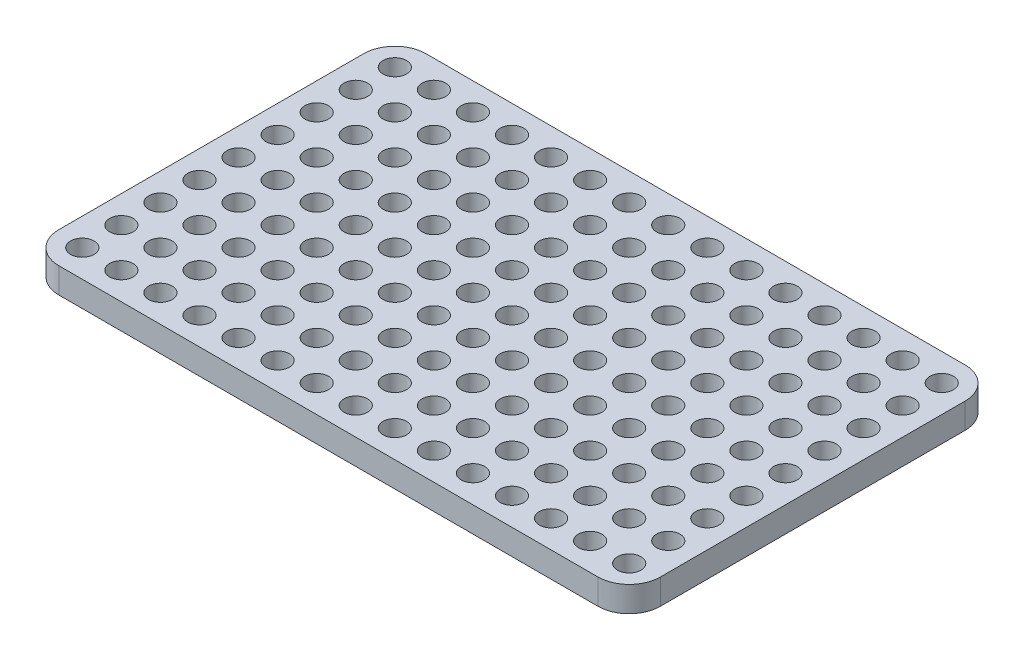
SolidWorks part; units mm, degrees
material "ABS"
ref_plane "Front Plane" through (0, 0, 0) normal (0, 0, 1) x (1, 0, 0)
ref_plane "Top Plane" through (0, 0, 0) normal (0, 1, 0) x (1, 0, 0)
ref_plane "Right Plane" through (0, 0, 0) normal (1, 0, 0) x (0, 0, -1)
sketch "Sketch1" plane through (0, 0, 0) normal (0, 1, 0) x (1, 0, 0)
  line L0 (-38.5, 23.5) -> (38.5, -23.5) construction
  line L1 (-34.5, 23.5) -> (34.5, 23.5)
  line L2 (-38.5, 19.5) -> (-38.5, -19.5)
  line L3 (-34.5, -23.5) -> (34.5, -23.5)
  line L4 (38.5, 19.5) -> (38.5, -19.5)
  circle A0 centre (-35, -20) radius 1.5025
  circle A1 centre (-30, -20) radius 1.5025
  circle A2 centre (-25, -20) radius 1.5025
  circle A3 centre (-20, -20) radius 1.5025
  circle A4 centre (-15, -20) radius 1.5025
  circle A5 centre (-10, -20) radius 1.5025
  circle A6 centre (-5, -20) radius 1.5025
  circle A7 centre (0, -20) radius 1.5025
  circle A8 centre (5, -20) radius 1.5025
  circle A9 centre (10, -20) radius 1.5025
  circle A10 centre (15, -20) radius 1.5025
  circle A11 centre (20, -20) radius 1.5025
  circle A12 centre (25, -20) radius 1.5025
  circle A13 centre (30, -20) radius 1.5025
  circle A14 centre (35, -20) radius 1.5025
  circle A15 centre (-35, -15) radius 1.5025
  circle A16 centre (-30, -15) radius 1.5025
  circle A17 centre (-25, -15) radius 1.5025
  circle A18 centre (-20, -15) radius 1.5025
  circle A19 centre (-15, -15) radius 1.5025
  circle A20 centre (-10, -15) radius 1.5025
  circle A21 centre (-5, -15) radius 1.5025
  circle A22 centre (0, -15) radius 1.5025
  circle A23 centre (5, -15) radius 1.5025
  circle A24 centre (10, -15) radius 1.5025
  circle A25 centre (15, -15) radius 1.5025
  circle A26 centre (20, -15) radius 1.5025
  circle A27 centre (25, -15) radius 1.5025
  circle A28 centre (30, -15) radius 1.5025
  circle A29 centre (35, -15) radius 1.5025
  circle A30 centre (-35, -10) radius 1.5025
  circle A31 centre (-30, -10) radius 1.5025
  circle A32 centre (-25, -10) radius 1.5025
  circle A33 centre (-20, -10) radius 1.5025
  circle A34 centre (-15, -10) radius 1.5025
  circle A35 centre (-10, -10) radius 1.5025
  circle A36 centre (-5, -10) radius 1.5025
  circle A37 centre (0, -10) radius 1.5025
  circle A38 centre (5, -10) radius 1.5025
  circle A39 centre (10, -10) radius 1.5025
  circle A40 centre (15, -10) radius 1.5025
  circle A41 centre (20, -10) radius 1.5025
  circle A42 centre (25, -10) radius 1.5025
  circle A43 centre (30, -10) radius 1.5025
  circle A44 centre (35, -10) radius 1.5025
  circle A45 centre (-35, -5) radius 1.5025
  circle A46 centre (-30, -5) radius 1.5025
  circle A47 centre (-25, -5) radius 1.5025
  circle A48 centre (-20, -5) radius 1.5025
  circle A49 centre (-15, -5) radius 1.5025
  circle A50 centre (-10, -5) radius 1.5025
  circle A51 centre (-5, -5) radius 1.5025
  circle A52 centre (0, -5) radius 1.5025
  circle A53 centre (5, -5) radius 1.5025
  circle A54 centre (10, -5) radius 1.5025
  circle A55 centre (15, -5) radius 1.5025
  circle A56 centre (20, -5) radius 1.5025
  circle A57 centre (25, -5) radius 1.5025
  circle A58 centre (30, -5) radius 1.5025
  circle A59 centre (35, -5) radius 1.5025
  circle A60 centre (-35, 0) radius 1.5025
  circle A61 centre (-30, 0) radius 1.5025
  circle A62 centre (-25, 0) radius 1.5025
  circle A63 centre (-20, 0) radius 1.5025
  circle A64 centre (-15, 0) radius 1.5025
  circle A65 centre (-10, 0) radius 1.5025
  circle A66 centre (-5, 0) radius 1.5025
  circle A67 centre (0, 0) radius 1.5025
  circle A68 centre (5, 0) radius 1.5025
  circle A69 centre (10, 0) radius 1.5025
  circle A70 centre (15, 0) radius 1.5025
  circle A71 centre (20, 0) radius 1.5025
  circle A72 centre (25, 0) radius 1.5025
  circle A73 centre (30, 0) radius 1.5025
  circle A74 centre (35, 0) radius 1.5025
  circle A75 centre (-35, 5) radius 1.5025
  circle A76 centre (-30, 5) radius 1.5025
  circle A77 centre (-25, 5) radius 1.5025
  circle A78 centre (-20, 5) radius 1.5025
  circle A79 centre (-15, 5) radius 1.5025
  circle A80 centre (-10, 5) radius 1.5025
  circle A81 centre (-5, 5) radius 1.5025
  circle A82 centre (0, 5) radius 1.5025
  circle A83 centre (5, 5) radius 1.5025
  circle A84 centre (10, 5) radius 1.5025
  circle A85 centre (15, 5) radius 1.5025
  circle A86 centre (20, 5) radius 1.5025
  circle A87 centre (25, 5) radius 1.5025
  circle A88 centre (30, 5) radius 1.5025
  circle A89 centre (35, 5) radius 1.5025
  circle A90 centre (-35, 10) radius 1.5025
  circle A91 centre (-30, 10) radius 1.5025
  circle A92 centre (-25, 10) radius 1.5025
  circle A93 centre (-20, 10) radius 1.5025
  circle A94 centre (-15, 10) radius 1.5025
  circle A95 centre (-10, 10) radius 1.5025
  circle A96 centre (-5, 10) radius 1.5025
  circle A97 centre (0, 10) radius 1.5025
  circle A98 centre (5, 10) radius 1.5025
  circle A99 centre (10, 10) radius 1.5025
  circle A100 centre (15, 10) radius 1.5025
  circle A101 centre (20, 10) radius 1.5025
  circle A102 centre (25, 10) radius 1.5025
  circle A103 centre (30, 10) radius 1.5025
  circle A104 centre (35, 10) radius 1.5025
  circle A105 centre (-35, 15) radius 1.5025
  circle A106 centre (-30, 15) radius 1.5025
  circle A107 centre (-25, 15) radius 1.5025
  circle A108 centre (-20, 15) radius 1.5025
  circle A109 centre (-15, 15) radius 1.5025
  circle A110 centre (-10, 15) radius 1.5025
  circle A111 centre (-5, 15) radius 1.5025
  circle A112 centre (0, 15) radius 1.5025
  circle A113 centre (5, 15) radius 1.5025
  circle A114 centre (10, 15) radius 1.5025
  circle A115 centre (15, 15) radius 1.5025
  circle A116 centre (20, 15) radius 1.5025
  circle A117 centre (25, 15) radius 1.5025
  circle A118 centre (30, 15) radius 1.5025
  circle A119 centre (35, 15) radius 1.5025
  circle A120 centre (-35, 20) radius 1.5025
  circle A121 centre (-30, 20) radius 1.5025
  circle A122 centre (-25, 20) radius 1.5025
  circle A123 centre (-20, 20) radius 1.5025
  circle A124 centre (-15, 20) radius 1.5025
  circle A125 centre (-10, 20) radius 1.5025
  circle A126 centre (-5, 20) radius 1.5025
  circle A127 centre (0, 20) radius 1.5025
  circle A128 centre (5, 20) radius 1.5025
  circle A129 centre (10, 20) radius 1.5025
  circle A130 centre (15, 20) radius 1.5025
  circle A131 centre (20, 20) radius 1.5025
  circle A132 centre (25, 20) radius 1.5025
  circle A133 centre (30, 20) radius 1.5025
  circle A134 centre (35, 20) radius 1.5025
  arc A135 (34.5, -23.5) -> (38.5, -19.5) centre (34.5, -19.5) ccw
  arc A136 (-38.5, -19.5) -> (-34.5, -23.5) centre (-34.5, -19.5) ccw
  arc A137 (-34.5, 23.5) -> (-38.5, 19.5) centre (-34.5, 19.5) ccw
  arc A138 (34.5, 23.5) -> (38.5, 19.5) centre (34.5, 19.5) cw
  point P285 (38.5, 23.5)
  dimension "D3" = 3.5
  dimension "D4" = 3.5
  dimension "D5" = 3.005
  dimension "D8" = 3.5
  dimension "D9" = 3.5
  dimension "D10" = 3.5
  dimension "D11" = 3.5
  dimension "D12" = 4
  dimension "D1" = 77
  dimension "D2" = 47
  dimension "D6" = 15
  dimension "D7" = 9
extrude "Boss-Extrude1" add sketch "Sketch1" along normal blind 3.25
